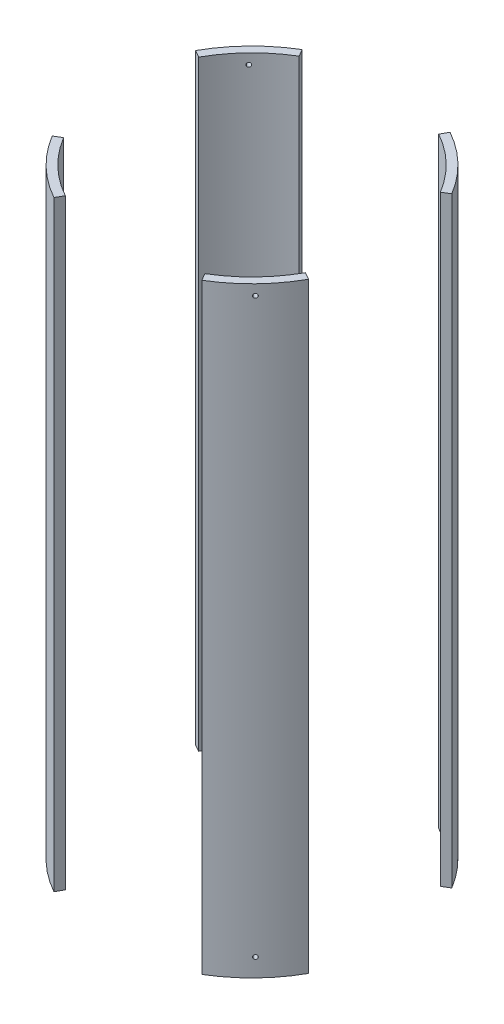
SolidWorks part; units mm, degrees
material "6061-T6 (SS)"
ref_plane "Front Plane" through (0, 0, 0) normal (0, 0, 1) x (1, 0, 0)
ref_plane "Top Plane" through (0, 0, 0) normal (0, 1, 0) x (1, 0, 0)
ref_plane "Right Plane" through (0, 0, 0) normal (1, 0, 0) x (0, 0, -1)
sketch "Sketch2" plane through (0, 0, 0) normal (0, 1, 0) x (1, 0, 0)
  circle A0 centre (0, 0) radius 88.9
  circle A1 centre (0, 0) radius 83.82
  dimension "D1" = 177.8
  dimension "D2" = 167.64
extrude "Boss-Extrude1" add sketch "Sketch2" along normal mid plane 366.9767
sketch "Sketch3" plane through (0, 0, 0) normal (0, 1, 0) x (1, 0, 0)
  line L0 (0, 0) -> (169.6618, 101.6776)
  line L1 (-58.1167, 96.9749) -> (0, 0)
  line L2 (0, 0) -> (53.9, 96.9749)
  line L3 (53.9, 96.9749) -> (-58.1167, 96.9749)
  line L4 (0, 0) -> (70.9917, -118.4586)
  line L5 (70.9917, -118.4586) -> (-65.8409, -118.4586)
  line L6 (-65.8409, -118.4586) -> (0, 0)
  line L7 (169.6618, 101.6776) -> (169.6618, -94.3004)
  line L8 (169.6618, -94.3004) -> (0, 0)
  line L9 (0, 0) -> (-123.7413, 68.7771)
  line L10 (-123.7413, 68.7771) -> (-123.7413, -74.1577)
  line L11 (-123.7413, -74.1577) -> (0, 0)
  dimension "D1" = 60
  dimension "D2" = 60
  dimension "D3" = 60
  dimension "D4" = 60
  dimension "D5" = 30
  dimension "D6" = 30
extrude "Cut-Extrude1" cut sketch "Sketch3" against normal through all both and the other way through all contours L8 L7 L0 | L2 L3 L1 | L10 L11 L9 | L6 L5 L4
ref_plane "Bolt reference plane" through (-56.3092, 0, 58.1758) normal (0.6955, 0, -0.7185) x (-0.7185, 0, -0.6955)
sketch "Sketch5" plane through (-56.3092, 0, 58.1758) normal (0.6955, 0, -0.7185) x (-0.7185, 0, -0.6955)
  line L0 (-23.009, -183.4883) -> (23.009, -183.4883) construction
  circle A0 centre (-0.0228, 177.1383) radius 1.27
  circle A1 centre (-0.0228, -172.3758) radius 1.27
  dimension "D1" = 2.54
  dimension "D4" = 11.1125
  dimension "D2" = 21.717
  dimension "D3" = 6.35
extrude "Bolt holes" cut sketch "Sketch5" against normal through all
pattern_circular "Bolt pattern" count 4 over 360 about axis through (0, 183.4883, 0) along (0, 1, 0) of "Bolt holes"
equation "\"D1@Boss-Extrude1\"=3*12"
